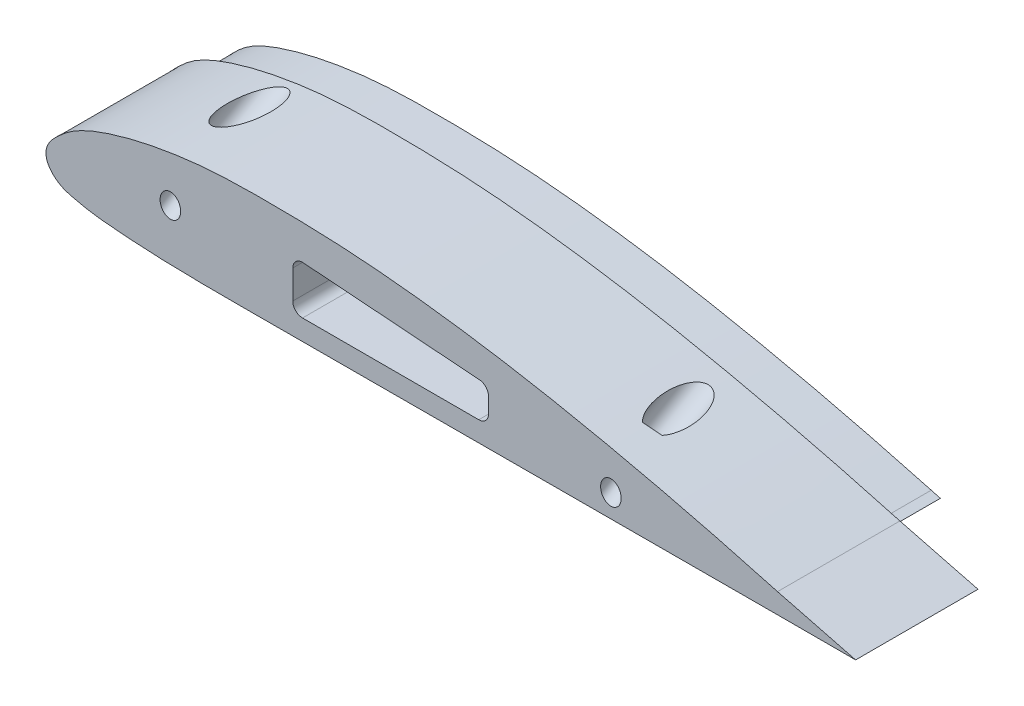
SolidWorks part; units mm, degrees
ref_plane "Front Plane" through (0, 0, 0) normal (0, 0, 1) x (1, 0, 0)
ref_plane "Top Plane" through (0, 0, 0) normal (0, 1, 0) x (1, 0, 0)
ref_plane "Right Plane" through (0, 0, 0) normal (1, 0, 0) x (0, 0, -1)
sketch "Sketch1" plane through (0, 0, 0) normal (0, 0, 1) x (1, 0, 0)
  line L4 (283.5115, 5) -> (300, 5)
  line L5 (300, 5) -> (284.0429, 9.1047)
  spline S2 degree 3 poles (284.0429, 9.1047) (281.0182, 9.9344) (274.9702, 11.5879) (262.7947, 14.6943) (247.4912, 18.2235) (228.9768, 21.8279) (213.3822, 24.0502) (200.838, 25.2782) (191.3752, 25.8437) (181.9292, 26.0327) (174.0455, 26.006) (167.6846, 25.6725) (162.9071, 25.1908) (158.1715, 24.4731) (154.2495, 23.6877) (151.1262, 22.9144) (148.8034, 22.2534) (146.5027, 21.5203) (144.1955, 20.6739) (142.2855, 19.8254) (140.7789, 19.0238) (139.6571, 18.333) (138.5799, 17.556) (137.5736, 16.6946) (136.8402, 16.0177) (136.1979, 15.3779) (135.7035, 14.8191) (135.2097, 14.1357) (134.8343, 13.4013) (134.6172, 12.6132) (134.5644, 11.9259) (134.6325, 11.2839) (134.8239, 10.646) (135.0503, 10.1715) (135.4024, 9.5941) (135.889, 9.014) (136.5032, 8.4537) (137.1891, 7.9612) (137.9344, 7.5673) (138.8878, 7.188) (139.9999, 6.8937) (141.1193, 6.6336) (142.3398, 6.3625) (143.5667, 6.1418) (145.2014, 5.9056) (147.2085, 5.702) (149.5549, 5.5018) (152.7201, 5.2635) (156.6645, 5.0546) (161.3946, 4.9004) (166.1151, 4.8221) (170.8269, 4.7935) (175.5318, 4.7968) (181.7926, 4.8194) (189.6121, 4.8333) (199.0042, 4.8461) (208.3936, 4.8645) (217.7834, 4.8816) (230.303, 4.9047) (245.9523, 4.9321) (264.7317, 4.9664) (277.2516, 4.9881) (283.5115, 5) knots 0 0 0 0 0.03125 0.0625 0.125 0.1875 0.25 0.28125 0.3125 0.34375 0.375 0.390625 0.40625 0.421875 0.4375 0.445312 0.453125 0.460938 0.46875 0.476562 0.480469 0.484375 0.488281 0.492188 0.496094 0.498047 0.5 0.501953 0.503906 0.504883 0.505859 0.506836 0.507812 0.508789 0.509766 0.511719 0.513672 0.515625 0.517578 0.519531 0.523438 0.527344 0.53125 0.535156 0.539062 0.546875 0.554688 0.5625 0.578125 0.59375 0.609375 0.625 0.640625 0.65625 0.6875 0.71875 0.75 0.78125 0.8125 0.875 0.9375 1 1 1 1
extrude "Boss-Extrude1" add sketch "Sketch1" along normal blind 25
sketch "Sketch2" plane through (0, 0, 25) normal (0, 0, 1) x (1, 0, 0)
  line L0 (283.5138, 7.176) -> (283.5077, 7)
  spline S1 degree 3 poles (283.5138, 7.176) (281.5719, 7.7087) (278.6602, 8.5075) (273.8037, 9.8057) (267.9783, 11.312) (262.1421, 12.7496) (255.3336, 14.3496) (248.5296, 15.8732) (237.8298, 18.0745) (225.1769, 20.3734) (211.4981, 22.2445) (201.7081, 23.1823) (192.8989, 23.7583) (187.0194, 23.95) (180.1574, 24.0138) (175.2497, 24.0043) (170.3385, 23.8312) (165.4154, 23.4617) (161.4718, 22.9737) (156.5308, 22.1318) (152.5638, 21.2602) (148.6188, 20.1142) (145.6144, 19.0989) (143.118, 18.0296) (141.124, 16.9205) (139.7091, 15.9185) (138.6393, 14.9581) (137.8213, 14.1846) (137.2992, 13.6166) (136.9099, 13.0649) (136.6947, 12.6285) (136.5581, 12.111) (136.5906, 11.6817) (136.7264, 11.3043) (136.876, 11.0027) (137.1856, 10.5599) (137.6647, 10.0852) (138.4186, 9.5356) (139.4995, 9.074) (140.8875, 8.7436) (142.3453, 8.4004) (143.8077, 8.1247) (145.7594, 7.8486) (148.2057, 7.6221) (151.1393, 7.3799) (157.0097, 7.007) (166.8124, 6.7551) (180.539, 6.8235) (193.287, 6.8363) (208.9776, 6.8654) (224.6681, 6.8944) (240.3587, 6.9228) (251.1459, 6.9412) (259.9719, 6.958) (268.7978, 6.973) (276.6431, 6.9879) (281.5464, 6.9963) (283.5077, 7) knots 0 0 0 0 0.020105 0.030145 0.050191 0.08018 0.090156 0.12002 0.149793 0.199219 0.248396 0.287604 0.297393 0.336535 0.346322 0.365908 0.385531 0.395376 0.415192 0.425184 0.445412 0.455711 0.466191 0.477055 0.482787 0.488946 0.494316 0.497126 0.500187 0.502001 0.50385 0.50502 0.507318 0.507987 0.509024 0.510668 0.513358 0.515716 0.519949 0.524973 0.529954 0.534903 0.539824 0.54963 0.559425 0.569214 0.608356 0.657307 0.706263 0.735637 0.813967 0.862923 0.892297 0.92167 0.951044 0.980418 1 1 1 1
extrude "Boss-Extrude2" add sketch "Sketch2" along normal blind 10
sketch "Sketch4" plane through (0, 0, 35) normal (0, 0, 1) x (1, 0, 0)
  line L0 (300, 5) -> (88.4314, 5) construction
  circle A0 centre (175, 15) radius 3.6
  circle A1 centre (238.5138, 12) radius 3.6
  dimension "D2" = 125
  dimension "D3" = 45
  dimension "D4" = 7
  dimension "D1" = 10
extrude "Cut-Extrude1" cut sketch "Sketch4" against normal blind 15 contours A0 | A1
sketch "Sketch5" plane through (0, 0, 35) normal (0, 0, 1) x (1, 0, 0)
  line L0 (185, 19) -> (185, 9)
  line L1 (185, 9) -> (225, 9)
  line L2 (225, 9) -> (225, 16)
  line L3 (225, 16) -> (185, 19)
  line L4 (300, 5) -> (100, 5) construction
  dimension "D1" = 10
  dimension "D2" = 4
  dimension "D3" = 7
  dimension "D4" = 75
  dimension "D5" = 40
extrude "Cut-Extrude3" cut sketch "Sketch5" against normal through all
fillet "Fillet1" radius 2 4 edges at (185, 19, 17.5) (185, 9, 17.5) (225, 16, 17.5) (225, 9, 17.5)
sketch "Sketch7" plane through (0, 0, 20) normal (0, 0, 1) x (1, 0, 0)
  circle A0 centre (238.5138, 12) radius 3.6 construction
  circle A1 centre (238.5138, 12) radius 3.6
  circle A2 centre (175, 15) radius 3.6
extrude "Cut-Extrude5" cut sketch "Sketch7" against normal blind 10
ref_plane "Plane1" through (160, 0, 0) normal (1, 0, 0) x (0, 0, -1)
sketch "Sketch8" plane through (160, 0, 0) normal (1, 0, 0) x (0, 0, -1)
  line L0 (-28.294, 31.7375) -> (0, 15.4019)
  line L2 (0, 4.7961) -> (0, 26.0077) construction
  line L3 (0, 15.4019) -> (-20.6135, 15.4019) construction
  dimension "D1" = 30
ref_plane "Plane2" through (160, 31.7375, 28.294) normal (0, -0.5, -0.866) x (-1, 0, 0)
sketch "Sketch9" plane through (160, 31.7375, 28.294) normal (0, -0.5, -0.866) x (-1, 0, 0)
  line L0 (0, 0) -> (0, -10.3067) construction
  line L1 (0, 0) -> (0, -5) construction
  line L2 (0, -5) -> (-90, -5) construction
  circle A0 centre (0, 0) radius 2.1
  circle A1 centre (-90, -5) radius 2.1
extrude "Cut-Extrude6" cut sketch "Sketch9" along normal through all
sketch "Sketch10" plane through (160, 31.7375, 28.294) normal (0, -0.5, -0.866) x (-1, 0, 0)
  circle A0 centre (0, 0) radius 3.5
  circle A1 centre (-90, -5) radius 3.5
extrude "Cut-Extrude7" cut sketch "Sketch10" along normal blind 25 contours A1 | A0
sketch "Sketch11" plane through (0, 0, 35) normal (0, 0, 1) x (1, 0, 0)
  line L0 (280.5134, 7.2445) -> (282.3112, 7.2477)
  line L3 (280.448, 7.7565) -> (282.3112, 7.2477)
  line L6 (283.5115, 5) -> (300, 5)
  line L7 (300, 5) -> (284.0429, 9.1047)
  line L8 (283.5115, 5) -> (300, 5)
  line L9 (300, 5) -> (284.0429, 9.1047)
  spline S2 degree 3 poles (2469.1253, 3330.2831) (578.7241, -152.5431) (439.4264, -30.371) (262.7947, 14.6943) (247.4912, 18.2235) (228.9768, 21.8279) (213.3822, 24.0502) (200.838, 25.2782) (191.3752, 25.8437) (181.9292, 26.0327) (174.0455, 26.006) (167.6846, 25.6725) (162.9071, 25.1908) (158.1715, 24.4731) (154.2495, 23.6877) (151.1262, 22.9144) (148.8034, 22.2534) (146.5027, 21.5203) (144.1955, 20.6739) (142.2855, 19.8254) (140.7789, 19.0238) (139.6571, 18.333) (138.5799, 17.556) (137.5736, 16.6946) (136.8402, 16.0177) (136.1979, 15.3779) (135.7035, 14.8191) (135.2097, 14.1357) (134.8343, 13.4013) (134.6172, 12.6132) (134.5644, 11.9259) (134.6325, 11.2839) (134.8239, 10.646) (135.0503, 10.1715) (135.4024, 9.5941) (135.889, 9.014) (136.5032, 8.4537) (137.1891, 7.9612) (137.9344, 7.5673) (138.8878, 7.188) (139.9999, 6.8937) (141.1193, 6.6336) (142.3398, 6.3625) (143.5667, 6.1418) (145.2014, 5.9056) (147.2085, 5.702) (149.5549, 5.5018) (152.7201, 5.2635) (156.6645, 5.0546) (161.3946, 4.9004) (166.1151, 4.8221) (170.8269, 4.7935) (175.5318, 4.7968) (181.7926, 4.8194) (189.6121, 4.8333) (199.0042, 4.8461) (208.3936, 4.8645) (217.7834, 4.8816) (230.303, 4.9047) (245.9523, 4.9321) (1062.3632, 6.4244) (1873.6845, 2.8543) (2454.3014, 2917.181) knots -1.688391 -1.688391 -1.688391 -1.688391 0.03125 0.0625 0.125 0.1875 0.25 0.28125 0.3125 0.34375 0.375 0.390625 0.40625 0.421875 0.4375 0.445312 0.453125 0.460938 0.46875 0.476562 0.480469 0.484375 0.488281 0.492188 0.496094 0.498047 0.5 0.501953 0.503906 0.504883 0.505859 0.506836 0.507812 0.508789 0.509766 0.511719 0.513672 0.515625 0.517578 0.519531 0.523438 0.527344 0.53125 0.535156 0.539062 0.546875 0.554688 0.5625 0.578125 0.59375 0.609375 0.625 0.640625 0.65625 0.6875 0.71875 0.75 0.78125 0.8125 0.875 0.9375 8.963818 8.963818 8.963818 8.963818 only from (284.0429, 9.1047) to (283.5115, 5)
  spline S3 degree 3 poles (280.448, 7.7565) (274.5345, 9.3714) (262.6663, 12.4565) (244.7251, 16.5) (229.6665, 19.3599) (217.5457, 21.1803) (208.4198, 22.2922) (199.2672, 23.1416) (190.0905, 23.6336) (180.8981, 23.7894) (173.2386, 23.7336) (167.1292, 23.3697) (162.5678, 22.8749) (158.0342, 22.1607) (153.5392, 21.2365) (149.8525, 20.2348) (146.9452, 19.2923) (144.8035, 18.4896) (142.7255, 17.5469) (141.0857, 16.5987) (139.8698, 15.7033) (139.0136, 14.961) (138.1704, 14.1822) (137.4011, 13.3736) (136.8033, 12.4442) (136.8299, 11.4518) (137.4826, 10.5655) (138.3295, 9.8695) (139.3297, 9.4073) (140.4153, 9.1074) (141.5373, 8.8472) (143.0221, 8.5123) (144.8994, 8.2037) (147.177, 7.9637) (149.4676, 7.7672) (152.5195, 7.5313) (156.3422, 7.3214) (160.9342, 7.1629) (165.53, 7.0792) (171.6595, 7.0342) (179.3241, 7.0622) (188.5242, 7.0825) (197.7228, 7.0937) (209.9881, 7.1177) (225.3196, 7.1455) (243.7176, 7.1784) (262.1155, 7.2115) (274.3808, 7.2336) (280.5134, 7.2445) knots 0.010352 0.010352 0.010352 0.010352 0.071582 0.132813 0.194043 0.224658 0.255273 0.285888 0.316503 0.347118 0.377734 0.393041 0.408349 0.423656 0.438964 0.454271 0.461925 0.469579 0.477233 0.484887 0.488713 0.49254 0.496367 0.500194 0.504021 0.507848 0.511675 0.515502 0.519329 0.523155 0.526982 0.530809 0.538463 0.546117 0.553771 0.561424 0.576732 0.592039 0.607347 0.622655 0.65327 0.683885 0.7145 0.745115 0.806345 0.867576 0.928806 0.990036 0.990036 0.990036 0.990036
  spline S4 degree 3 poles (284.0429, 9.1047) (281.0182, 9.9344) (274.9702, 11.5879) (262.7947, 14.6943) (247.4912, 18.2235) (228.9768, 21.8279) (213.3822, 24.0502) (200.838, 25.2782) (191.3752, 25.8437) (181.9292, 26.0327) (174.0455, 26.006) (167.6846, 25.6725) (162.9071, 25.1908) (158.1715, 24.4731) (154.2495, 23.6877) (151.1262, 22.9144) (148.8034, 22.2534) (146.5027, 21.5203) (144.1955, 20.6739) (142.2855, 19.8254) (140.7789, 19.0238) (139.6571, 18.333) (138.5799, 17.556) (137.5736, 16.6946) (136.8402, 16.0177) (136.1979, 15.3779) (135.7035, 14.8191) (135.2097, 14.1357) (134.8343, 13.4013) (134.6172, 12.6132) (134.5644, 11.9259) (134.6325, 11.2839) (134.8239, 10.646) (135.0503, 10.1715) (135.4024, 9.5941) (135.889, 9.014) (136.5032, 8.4537) (137.1891, 7.9612) (137.9344, 7.5673) (138.8878, 7.188) (139.9999, 6.8937) (141.1193, 6.6336) (142.3398, 6.3625) (143.5667, 6.1418) (145.2014, 5.9056) (147.2085, 5.702) (149.5549, 5.5018) (152.7201, 5.2635) (156.6645, 5.0546) (161.3946, 4.9004) (166.1151, 4.8221) (170.8269, 4.7935) (175.5318, 4.7968) (181.7926, 4.8194) (189.6121, 4.8333) (199.0042, 4.8461) (208.3936, 4.8645) (217.7834, 4.8816) (230.303, 4.9047) (245.9523, 4.9321) (264.7317, 4.9664) (277.2516, 4.9881) (283.5115, 5) knots 0 0 0 0 0.03125 0.0625 0.125 0.1875 0.25 0.28125 0.3125 0.34375 0.375 0.390625 0.40625 0.421875 0.4375 0.445312 0.453125 0.460938 0.46875 0.476562 0.480469 0.484375 0.488281 0.492188 0.496094 0.498047 0.5 0.501953 0.503906 0.504883 0.505859 0.506836 0.507812 0.508789 0.509766 0.511719 0.513672 0.515625 0.517578 0.519531 0.523438 0.527344 0.53125 0.535156 0.539062 0.546875 0.554688 0.5625 0.578125 0.59375 0.609375 0.625 0.640625 0.65625 0.6875 0.71875 0.75 0.78125 0.8125 0.875 0.9375 1 1 1 1
  dimension "D1" = 0
extrude "Cut-Extrude8" cut sketch "Sketch11" against normal up to surface (10 mm away) up to face at (289.2734, 7.0524, 25)
mirror "Mirror1" about plane through (0, 0, 0) normal (0, 0, 1) of bodies 112
delete or keep bodies "Body-Delete/Keep 1" type delete bodies bodies 112
